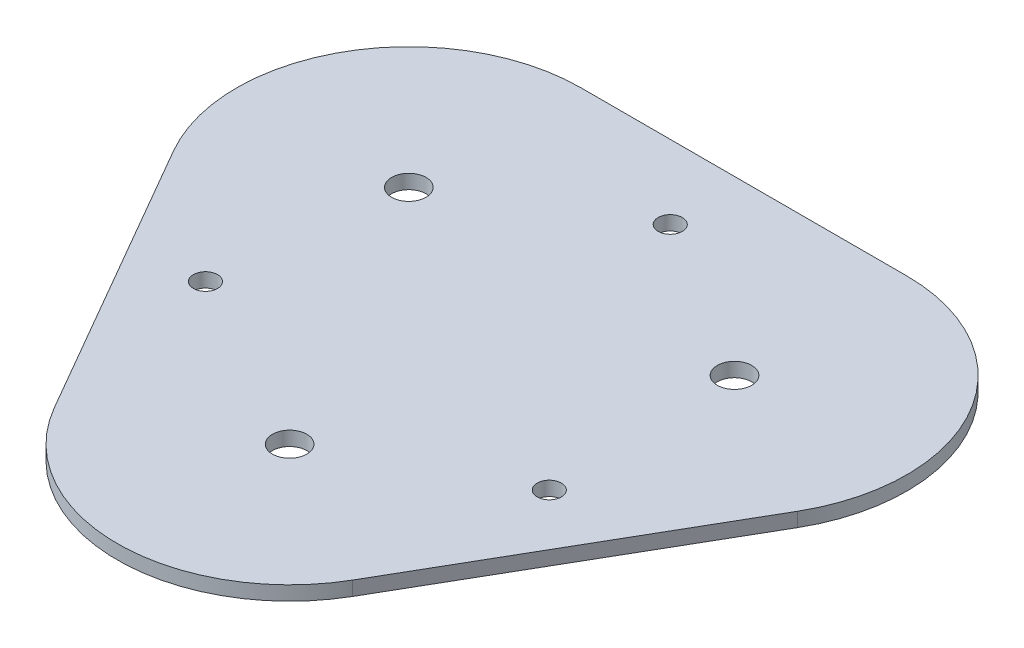
SolidWorks part; units mm, degrees
ref_plane "Front Plane" through (0, 0, 0) normal (0, 0, 1) x (1, 0, 0)
ref_plane "Top Plane" through (0, 0, 0) normal (0, 1, 0) x (1, 0, 0)
ref_plane "Right Plane" through (0, 0, 0) normal (1, 0, 0) x (0, 0, -1)
sketch "Sketch1" plane through (0, 0, 0) normal (0, 1, 0) x (1, 0, 0)
  line L0 (-18.9035, 10.9139) -> (18.9035, 10.9139) construction
  line L1 (-18.9035, 10.9139) -> (0, -21.8279) construction
  line L2 (36.224, 0.9139) -> (17.3205, -31.8279)
  line L3 (-36.224, 0.9139) -> (-17.3205, -31.8279)
  line L4 (-18.9035, 30.9139) -> (18.9035, 30.9139)
  line L5 (0, 0) -> (0, 22.3558) construction
  line L6 (0, 0) -> (-21.2385, -10.3587) construction
  line L7 (18.9035, 10.9139) -> (0, -21.8279) construction
  line L8 (0, 0) -> (19.6803, -11.3624) construction
  circle A0 centre (0, 0) radius 21.8279 construction
  circle A1 centre (-18.9035, 10.9139) radius 2
  circle A2 centre (18.9035, 10.9139) radius 2
  circle A3 centre (0, -21.8279) radius 2
  arc A4 (-18.9035, 30.9139) -> (-36.224, 0.9139) centre (-18.9035, 10.9139) ccw
  circle A5 centre (-21.2385, -10.3587) radius 1.4
  arc A6 (-17.3205, -31.8279) -> (17.3205, -31.8279) centre (0, -21.8279) ccw
  circle A7 centre (19.6803, -11.3624) radius 1.4
  circle A8 centre (0, 22.3558) radius 1.4
  arc A9 (36.224, 0.9139) -> (18.9035, 30.9139) centre (18.9035, 10.9139) ccw
  dimension "D4" = 4
  dimension "D5" = 4
  dimension "D6" = 4
  dimension "D7" = 40
  dimension "D9" = 40
  dimension "D8" = 2.8
  dimension "D11" = 2.8
  dimension "D13" = 2.8
  dimension "D1" = 37.807
  dimension "D2" = 37.807
  dimension "D3" = 37.807
  dimension "D10" = 116
  dimension "D12" = 124
  dimension "D14" = 23.63
  dimension "D15" = 22.3558
  dimension "D16" = 22.7248
extrude "Boss-Extrude1" add sketch "Sketch1" along normal blind 1.65
sketch "Sketch2" plane through (0, 0, 0) normal (0, -1, 0) x (1, 0, 0)
  line L0 (-2.5, 1.5) -> (2.5, 1.5)
  line L1 (2.5, 1.5) -> (2.5, -1.5)
  line L2 (2.5, -1.5) -> (-2.5, -1.5)
  line L3 (-2.5, -1.5) -> (-2.5, 1.5)
  point P5 (2.5, 0)
  dimension "D1" = 2.5
  dimension "D2" = 3
  dimension "D3" = 1.5
  dimension "D4" = 5
extrude "Boss-Extrude2" add sketch "Sketch2" along normal blind 4 contours L0 L1 L2 L3
equation "\"thread_diameter\"= 2.8"
equation "\"D13@Sketch1\"=\"thread_diameter\""
equation "\"D11@Sketch1\"=\"thread_diameter\""
equation "\"D8@Sketch1\"=\"thread_diameter\""
